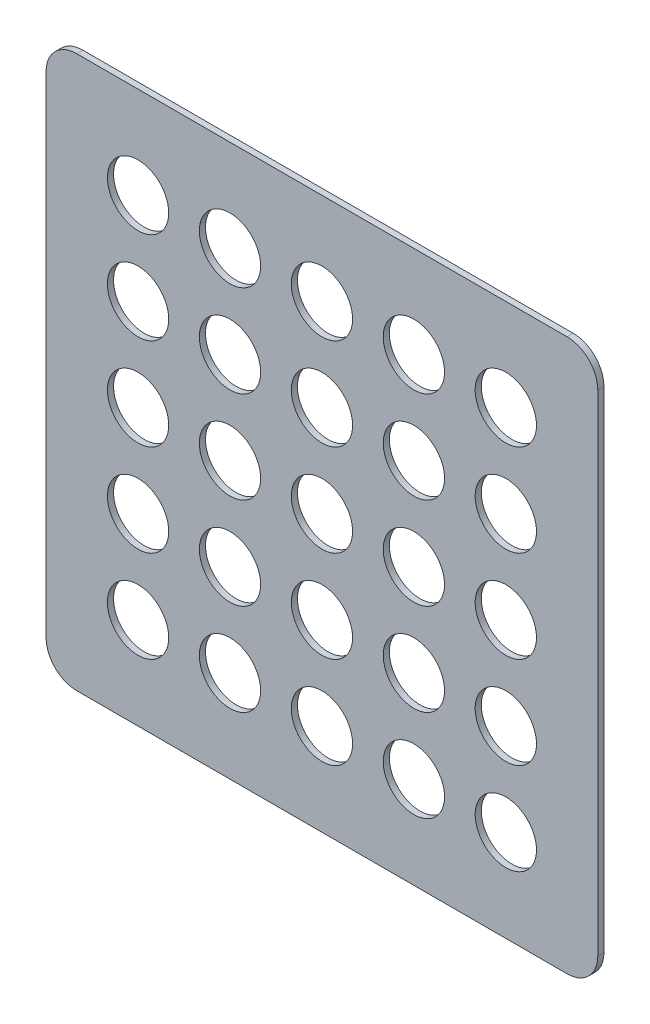
SolidWorks part; units mm, degrees
ref_plane "Front Plane" through (0, 0, 0) normal (0, 0, 1) x (1, 0, 0)
ref_plane "Top Plane" through (0, 0, 0) normal (0, 1, 0) x (1, 0, 0)
ref_plane "Right Plane" through (0, 0, 0) normal (1, 0, 0) x (0, 0, -1)
sketch "Sketch1" plane through (0, 0, 0) normal (0, 0, 1) x (1, 0, 0)
  line L1 (-2.25, -2.25) -> (2.25, -2.25)
  line L2 (-2.25, -2.25) -> (-2.25, 2.25)
  line L3 (-2.25, 2.25) -> (2.25, 2.25)
  line L4 (2.25, -2.25) -> (2.25, 2.25)
  line L5 (-2.25, -2.25) -> (2.25, 2.25) construction
  line L6 (-2.25, 2.25) -> (2.25, -2.25) construction
  point P0 (0, 0)
  dimension "D1" = 4.5
extrude "Boss-Extrude1" add sketch "Sketch1" along normal blind 0.05
fillet "Fillet1" radius 0.25 4 edges at (2.25, -2.25, 0.025) (-2.25, -2.25, 0.025) (-2.25, 2.25, 0.025) (2.25, 2.25, 0.025)
sketch "Sketch2" plane through (0, 0, 0.05) normal (0, 0, 1) x (1, 0, 0)
  circle A0 centre (0, 0) radius 0.25
  circle A1 centre (0.75, 0) radius 0.25
  circle A2 centre (1.5, 0) radius 0.25
  circle A3 centre (0.75, 0.75) radius 0.25
  circle A4 centre (1.5, 0.75) radius 0.25
  circle A5 centre (0.75, 1.5) radius 0.25
  circle A6 centre (1.5, 1.5) radius 0.25
  circle A7 centre (0, 0.75) radius 0.25
  circle A8 centre (0, 1.5) radius 0.25
  circle A9 centre (0.75, 0) radius 0.25
  circle A10 centre (1.5, 0) radius 0.25
  circle A11 centre (1.5, -0.75) radius 0.25
  circle A12 centre (0.75, -0.75) radius 0.25
  circle A13 centre (0.75, -1.5) radius 0.25
  circle A14 centre (0, -1.5) radius 0.25
  circle A15 centre (0, -0.75) radius 0.25
  circle A16 centre (1.5, -1.5) radius 0.25
  circle A17 centre (0, -0.75) radius 0.25
  circle A18 centre (0, -1.5) radius 0.25
  circle A19 centre (-0.75, -1.5) radius 0.25
  circle A20 centre (-0.75, -0.75) radius 0.25
  circle A21 centre (-1.5, -0.75) radius 0.25
  circle A22 centre (-1.5, 0) radius 0.25
  circle A23 centre (-0.75, 0) radius 0.25
  circle A24 centre (-1.5, -1.5) radius 0.25
  circle A25 centre (-0.75, 0) radius 0.25
  circle A26 centre (-1.5, 0) radius 0.25
  circle A27 centre (-1.5, 0.75) radius 0.25
  circle A28 centre (-0.75, 0.75) radius 0.25
  circle A29 centre (-0.75, 1.5) radius 0.25
  circle A30 centre (0, 1.5) radius 0.25
  circle A31 centre (0, 0.75) radius 0.25
  circle A32 centre (-1.5, 1.5) radius 0.25
  dimension "D1" = 0.5
  dimension "D2" = 3
  dimension "D3" = 3
  dimension "D4" = 4
extrude "Cut-Extrude1" cut sketch "Sketch2" against normal blind 0.05 contours A22 | A27 | A32 | A29 | A8 | A5 | A6 | A4 | A3 | A7 | A28 | A23 | A0 | A1 | A2 | A11 | A16 | A13 | A12 | A14 | A15 | A20 | A19 | A24 | A21
sketch "Sketch3" [suppressed] plane through (0, 0, 0.05) normal (0, 0, 1) x (1, 0, 0)
  line L0 (-1.25, 2.25) -> (-1.25, -1.25)
  line L1 (2, 2.25) -> (-2, 2.25) construction
  line L2 (-1.25, -1.25) -> (-0.5, -1.25)
  line L3 (-0.5, -1.25) -> (-0.5, 1.75)
  line L4 (-0.5, 1.75) -> (1.25, 1.75)
  line L5 (1.25, 1.75) -> (1.25, -1.25)
  line L6 (1.25, -1.25) -> (1.9871, -1.25)
  line L10 (-2, -2.25) -> (2, -2.25) construction
  line L11 (-1.75, 2.25) -> (-1.75, -1.75)
  line L12 (-1.75, -1.75) -> (0, -1.75)
  line L13 (0, -1.75) -> (0, 1.25)
  line L14 (0, 1.25) -> (0.75, 1.25)
  line L15 (0.75, 1.25) -> (0.75, -1.75)
  line L16 (0.75, -1.75) -> (1.7987, -1.75)
  line L21 (-1.75, 2.25) -> (-1.25, 2.25)
  line L22 (-2.25, 2) -> (-2.25, -2) construction
  line L23 (1.7987, -1.75) -> (2.75, -1.75)
  line L24 (2.75, -1.75) -> (2.75, -1.25)
  line L25 (2.75, -1.25) -> (1.9871, -1.25)
  dimension "D1" = 0.5
  dimension "D2" = 0.5
  dimension "D3" = 0.75
  dimension "D4" = 1.75
  dimension "D5" = 0.5
  dimension "D6" = 0.5
  dimension "D7" = 0.5
  dimension "D8" = 0.5
  dimension "D9" = 0.75
  dimension "D10" = 1.75
  dimension "D11" = 0.5
  dimension "D12" = 0.5
  dimension "D13" = 1.5
extrude "Cut-Extrude2" [suppressed] cut sketch "Sketch3" against normal through all
sketch "Sketch4" [suppressed] plane through (0, 0, 0.05) normal (0, 0, 1) x (1, 0, 0)
  line L0 (0, -0.25) -> (0, 0)
  line L1 (-2.5, 0) -> (2.5, 0)
  line L2 (-2.5, -0.25) -> (2.5, -0.25)
  line L3 (-2.5, -0.25) -> (-2.5, 0.25)
  line L4 (-2.5, 0.25) -> (2.5, 0.25)
  line L5 (2.5, -0.25) -> (2.5, 0.25)
  line L6 (-2.5, -0.25) -> (2.5, 0.25) construction
  line L7 (-2.5, 0.25) -> (2.5, -0.25) construction
  line L9 (2.5, -0.5) -> (-2.5, -0.5)
  line L10 (2.5, -0.5) -> (2.5, 0.5)
  line L11 (2.5, 0.5) -> (-2.5, 0.5)
  line L12 (-2.5, -0.5) -> (-2.5, 0.5)
  line L13 (2.5, -0.5) -> (-2.5, 0.5) construction
  line L14 (2.5, 0.5) -> (-2.5, -0.5) construction
  circle A0 centre (0, 0) radius 2
  circle A1 centre (0, 0) radius 1.75
  circle A2 centre (0, 0) radius 1.5
  circle A3 centre (0, 0) radius 1.25
  circle A4 centre (0, 0) radius 1
  circle A5 centre (0, 0) radius 0.75
  circle A6 centre (0, 0) radius 0.5
  circle A7 centre (0, 0) radius 0.25
  point P18 (0, 0)
  line M8 (-2.25, 2) -> (-2.25, -2)
  dimension "D1" = 4
  dimension "D2" = 3.5
  dimension "D3" = 3
  dimension "D4" = 2.5
  dimension "D5" = 2
  dimension "D6" = 1.5
  dimension "D7" = 1
  dimension "D8" = 0.5
  dimension "D9" = 0.5
  dimension "D10" = 5
  dimension "D11" = 1
  dimension "D12" = 5
extrude "Cut-Extrude3" [suppressed] cut sketch "Sketch4" against normal through all contours A7 L2 A6 L1 | A7 L1 A6 L4 | L4 A6 | A7 L4 A6 L1 | A6 L4 A5 L1 | A5 L4 A4 L1 | A5 L11 A4 L4 | A5 L11 A4 | A5 L4 A4 L11 | A5 L1 A4 L4 | A5 L2 A4 L1 | A5 L9 A4 L2 | A5 L9 A4 | A5 L2 A4 L9 | A4 L2 A3 L9 | A3 L2 A2 L9 | A3 L11 A2 L4 | A3 L11 A2 | A3 L4 A2 L11 | A3 L1 A2 L4 | A3 L2 A2 L1 | A3 L9 A2 L2 | A1 L9 A0 L2 | A1 L9 A0 | A1 L2 A0 L9 | A1 L1 A0 L2 | A1 L11 A0 L4 | A1 L11 A0 | A1 L4 A0 L11 | A1 L1 A0 L4 | L2 A6 | A3 L9 A2 | A2 L11 A1 L4 | A1 L2 A0 L1 | L3 L2 L1 M8 | A0 L1 L2 M8
fillet "Fillet2" [suppressed] radius 0.125
fillet "Fillet3" [suppressed] radius 0.25
fillet "Fillet4" [suppressed] radius 0.25
